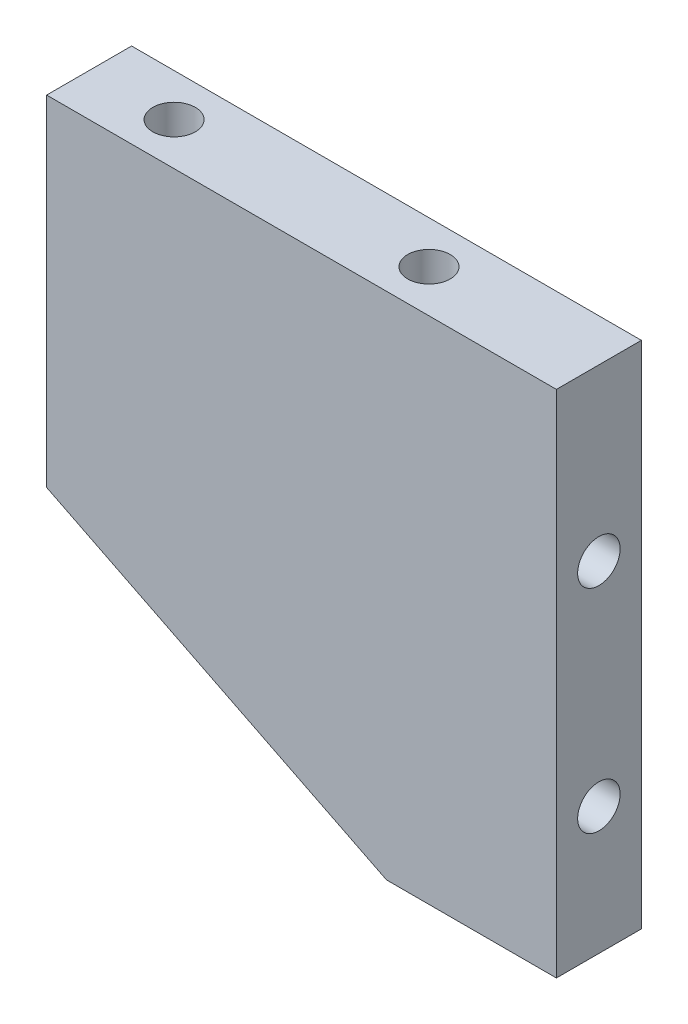
SolidWorks part; units mm, degrees
material "A3钢"
ref_plane "前视基准面" through (0, 0, 0) normal (0, 0, 1) x (1, 0, 0)
ref_plane "上视基准面" through (0, 0, 0) normal (0, 1, 0) x (1, 0, 0)
ref_plane "右视基准面" through (0, 0, 0) normal (1, 0, 0) x (0, 0, -1)
sketch "草图1" plane through (0, 0, 0) normal (0, 0, 1) x (1, 0, 0)
  line L0 (0, 0) -> (-60, 0)
  line L1 (-60, 0) -> (-60, -40)
  line L2 (-60, -40) -> (-20, -60)
  line L3 (-20, -60) -> (0, -60)
  line L4 (0, -60) -> (0, 0)
  dimension "D1" = 60
  dimension "D2" = 60
  dimension "D3" = 20
  dimension "D4" = 40
extrude "凸台-拉伸1" add sketch "草图1" along normal mid plane 10
sketch "草图2" plane through (0, 0, 0) normal (1, 0, 0) x (0, 0, -1)
  line L0 (0, 0) -> (0, -20) construction
  line L1 (-5, 0) -> (5, 0) construction
  line L2 (0, -20) -> (0, -45) construction
  dimension "D1" = 20
  dimension "D2" = 25
hole_wizard "M6 螺纹孔1" positions "3D草图1" profile "草图3" tap size "M6" standard "GB"
sketch3d "3D草图1"
  point P0 (0, -20, 0)
  point P7 (0, -45, 0)
sketch "草图3" plane through (0, -20, 0) normal (0, 1, 0) x (0, 0, -1)
  line L0 (0, 0) -> (0, 16.5022)
  line L1 (0, 16.5022) -> (2.5, 15)
  line L2 (2.5, 15) -> (2.5, 0)
  line L5 (2.5, 0) -> (0, 0)
  line L10 (0, 16.5022) -> (-2.5, 15) construction
  line L11 (0, -6.35) -> (0, 107.95) construction
  dimension "螺纹孔钻头直径" = 5
  dimension "螺纹孔钻头深度" = 15
  dimension "导头角度" = 118
cosmetic thread "孔螺蚊线1" parameters "D1"=12, "D2"=6
cosmetic thread "孔螺蚊线3" parameters "D1"=12, "D2"=6
sketch "草图4" plane through (0, 0, 0) normal (0, 1, 0) x (1, 0, 0)
  line L0 (0, 0) -> (-20, 0) construction
  line L1 (-20, 0) -> (-50, 0) construction
  dimension "D1" = 20
  dimension "D2" = 30
hole_wizard "M6 螺纹孔2" positions "3D草图2" profile "草图5" tap size "M6" standard "GB"
sketch3d "3D草图2"
  point P0 (-20, 0, 0)
  point P3 (-50, 0, 0)
sketch "草图5" plane through (-20, 0, 0) normal (1, 0, 0) x (0, 0, 1)
  line L0 (0, 0) -> (0, 16.5022)
  line L1 (0, 16.5022) -> (2.5, 15)
  line L2 (2.5, 15) -> (2.5, 0)
  line L5 (2.5, 0) -> (0, 0)
  line L10 (0, 16.5022) -> (-2.5, 15) construction
  line L11 (0, -6.35) -> (0, 107.95) construction
  dimension "螺纹孔钻头直径" = 5
  dimension "螺纹孔钻头深度" = 15
  dimension "导头角度" = 118
cosmetic thread "孔螺蚊线2" parameters "D1"=12, "D2"=6
cosmetic thread "孔螺蚊线4" parameters "D1"=12, "D2"=6
